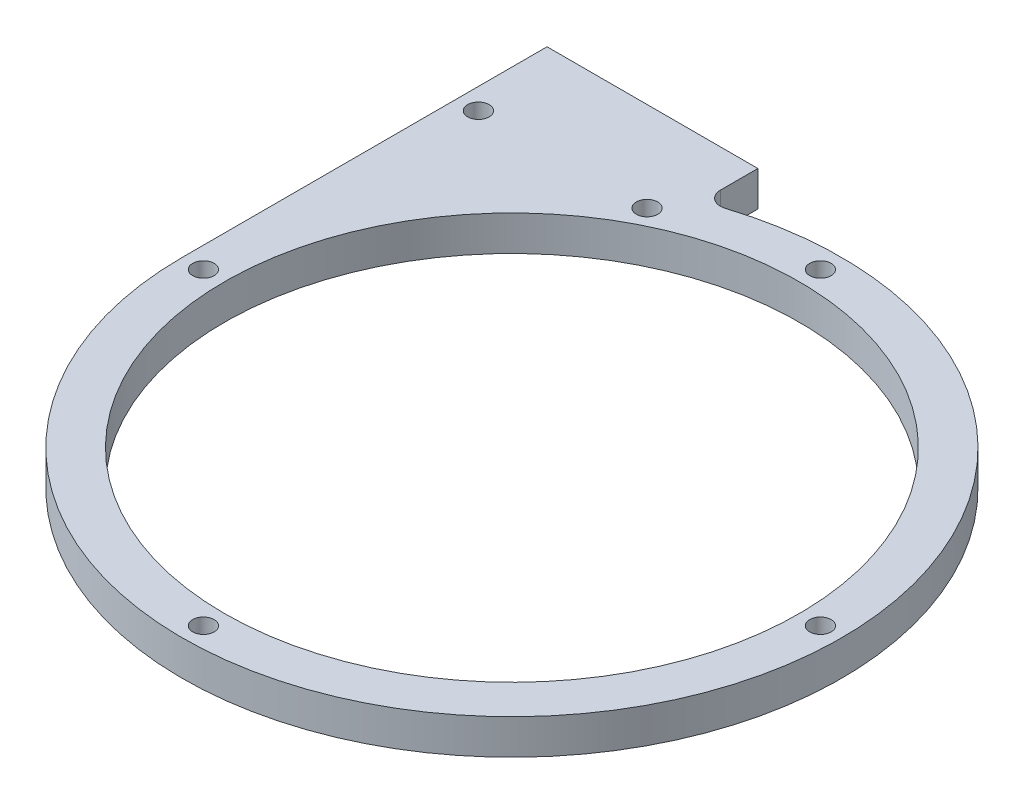
SolidWorks part; units mm, degrees
material "Thornel Mat VMA"
ref_plane "前视基准面" through (0, 0, 0) normal (0, 0, 1) x (1, 0, 0)
ref_plane "上视基准面" through (0, 0, 0) normal (0, 1, 0) x (1, 0, 0)
ref_plane "右视基准面" through (0, 0, 0) normal (1, 0, 0) x (0, 0, -1)
sketch "草图1" plane through (0, 0, 0) normal (0, 1, 0) x (1, 0, 0)
  line L0 (-46.9, 0) -> (-46.9, 46.9)
  line L1 (-46.9, 46.9) -> (-16.9, 46.9)
  line L2 (-16.9, 46.9) -> (-16.9, 46.5747)
  line L3 (-31.9, 0) -> (-31.9, 46.9) construction
  line L4 (-19.9, 46.9) -> (-19.9, 39.1306) construction
  line L5 (-19.9, 46.9) -> (-19.9, 43.7493) construction
  line L6 (-43.9, 0) -> (-43.9, 46.9) construction
  line L7 (-16.9, 46.9) -> (-16.9, 43.7493) construction
  arc A0 (-46.9, 0) -> (-14.2906, 44.6698) centre (0, 0) ccw
  circle A1 centre (0, 0) radius 40.9
  circle A2 centre (0, 0) radius 31.9 construction
  circle A4 centre (0, 0) radius 43.9 construction
  circle A5 centre (-19.9, 39.1306) radius 1.525
  circle A6 centre (0, 43.9) radius 1.525
  circle A7 centre (43.9, 0) radius 1.525
  circle A8 centre (0, -43.9) radius 1.525
  circle A9 centre (-43.9, 0) radius 1.525
  circle A20 centre (0, 0) radius 46.9 construction
  circle A21 centre (-43.9, 39.1306) radius 1.525
  arc A22 (-16.9, 46.5747) -> (-14.2906, 44.6698) centre (-14.9, 46.5747) ccw
  circle A24 centre (39.0795, -20) radius 1.525 construction
  dimension "D1" = 93.8
  dimension "D8" = 3.05
  dimension "D9" = 20
  dimension "D4" = 2
  dimension "D2" = 6
  dimension "D3" = 9
  dimension "D5" = 3
  dimension "D6" = 3
  dimension "D7" = 4
extrude "凸台-拉伸1" add sketch "草图1" along normal blind 5
sketch "草图3" plane through (0, 0, 0) normal (0, 1, 0) x (1, 0, 0)
  line L1 (-46.9, 46.9) -> (-16.9, 46.9)
  line L2 (-46.9, 46.9) -> (-46.9, 51.9)
  line L3 (-46.9, 51.9) -> (-16.9, 51.9)
  line L4 (-16.9, 46.9) -> (-16.9, 51.9)
  dimension "D1" = 5
extrude "凸台-拉伸2" add sketch "草图3" along normal blind 5
